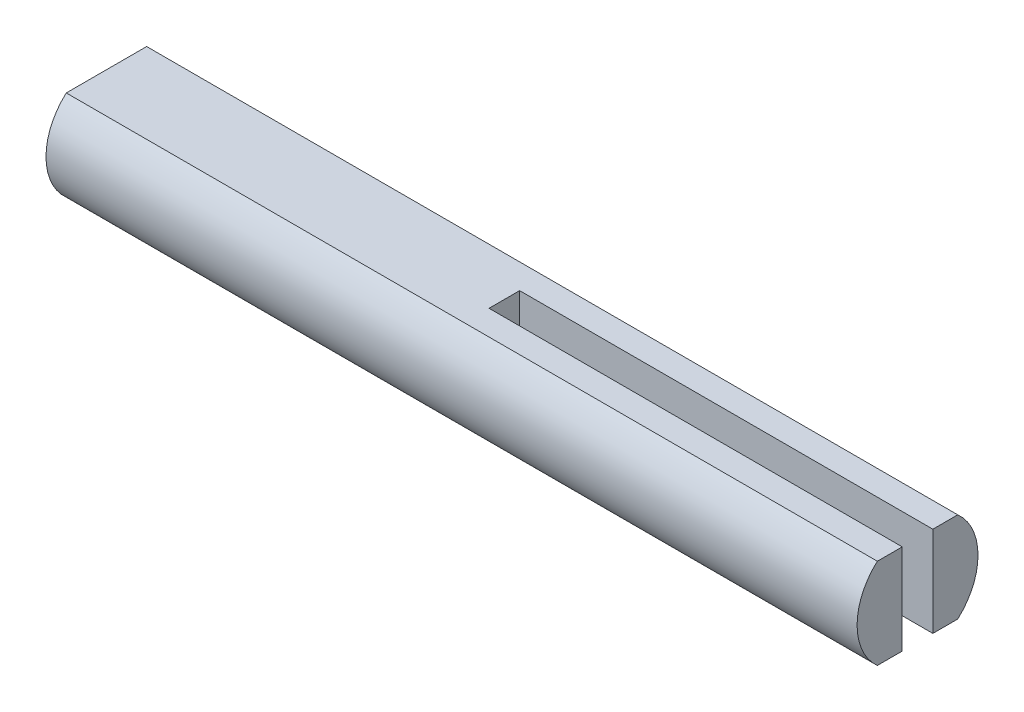
SolidWorks part; units mm, degrees
ref_plane "Front Plane" through (0, 0, 0) normal (0, 0, 1) x (1, 0, 0)
ref_plane "Top Plane" through (0, 0, 0) normal (0, 1, 0) x (1, 0, 0)
ref_plane "Right Plane" through (0, 0, 0) normal (1, 0, 0) x (0, 0, -1)
sketch "Sketch1" plane through (0, 0, 0) normal (1, 0, 0) x (0, 0, -1)
  line L2 (-2.6268, 2.95) -> (2.6268, 2.95)
  line L3 (-2.6268, -2.95) -> (2.6268, -2.95)
  arc A0 (2.6268, -2.95) -> (2.6268, 2.95) centre (0, 0) ccw
  arc A1 (-2.6268, 2.95) -> (-2.6268, -2.95) centre (0, 0) ccw
extrude "Boss-Extrude1" add sketch "Sketch1" along normal blind 40.5 and the other way blind 12.5
sketch "Sketch5" plane through (0, 2.95, 0) normal (0, 1, 0) x (1, 0, 0)
  line L0 (40.5, 0) -> (40.5, 1)
  line L1 (40.5, 2.6268) -> (40.5, -2.6268) construction
  line L2 (40.5, 1) -> (13.5, 1)
  line L4 (13.5, -1) -> (40.5, -1)
  line L5 (40.5, -1) -> (40.5, 0)
  line L10 (13.5, -1) -> (13.5, 1)
extrude "Cut-Extrude2" cut sketch "Sketch5" against normal through all
